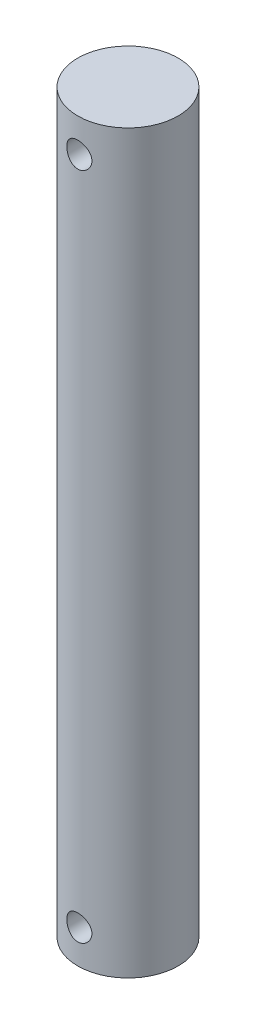
SolidWorks part; units mm, degrees
ref_plane "Front Plane" through (0, 0, 0) normal (0, 0, 1) x (1, 0, 0)
ref_plane "Top Plane" through (0, 0, 0) normal (0, 1, 0) x (1, 0, 0)
ref_plane "Right Plane" through (0, 0, 0) normal (1, 0, 0) x (0, 0, -1)
sketch "Sketch1" plane through (0, 0, 0) normal (0, 1, 0) x (1, 0, 0)
  circle A0 centre (0, 0) radius 19.05
  dimension "D1" = 38.1
extrude "Boss-Extrude1" add sketch "Sketch1" along normal blind 279.4
sketch "Sketch2" plane through (0, 0, 0) normal (0, 0, 1) x (1, 0, 0)
  line L1 (0, 0) -> (0, 279.4) construction
  line L2 (0, 139.7) -> (-19.05, 139.7) construction
  line L3 (-19.05, 279.4) -> (-19.05, 0) construction
  circle A0 centre (0, 266.7) radius 4.7625
  circle A1 centre (0, 12.7) radius 4.7625
  dimension "D1" = 9.525
  dimension "D2" = 12.7
extrude "Cut-Extrude1" cut sketch "Sketch2" against normal through all and the other way through all
